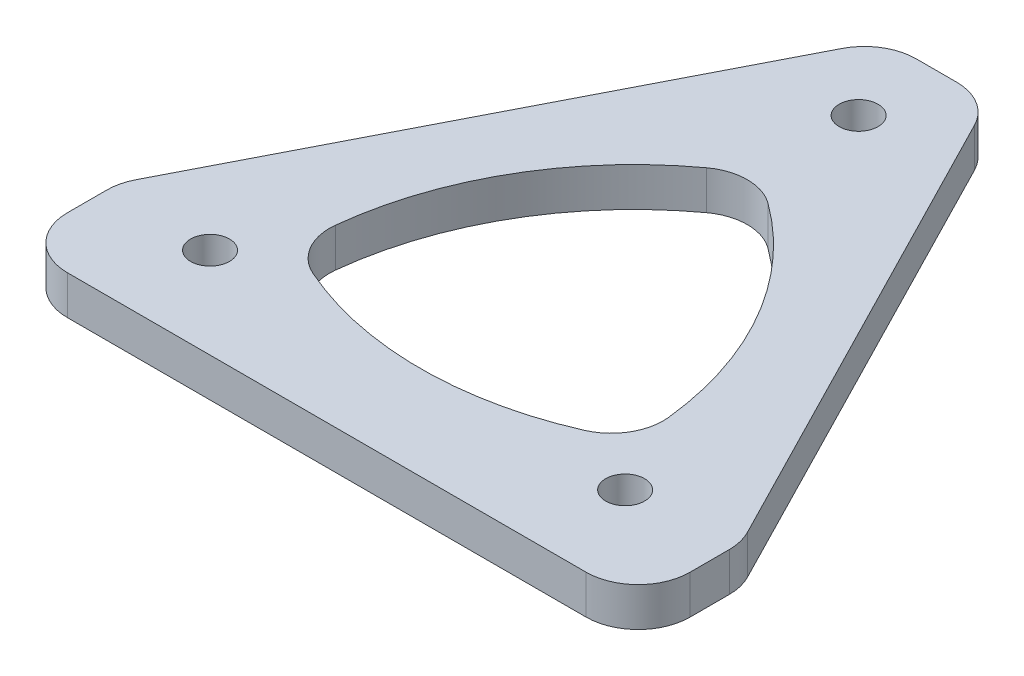
SolidWorks part; units mm, degrees
ref_plane "Front Plane" through (0, 0, 0) normal (0, 0, 1) x (1, 0, 0)
ref_plane "Top Plane" through (0, 0, 0) normal (0, 1, 0) x (1, 0, 0)
ref_plane "Right Plane" through (0, 0, 0) normal (1, 0, 0) x (0, 0, -1)
sketch "Sketch1" plane through (0, 0, 0) normal (0, 1, 0) x (1, 0, 0)
  line L0 (0, 0) -> (-20, 0)
  line L1 (-24, 4) -> (-24, 7.0342)
  line L8 (-23.5593, 8.8594) -> (-5.1152, 44.8253)
  line L10 (-1.556, 47) -> (1.556, 47)
  line L11 (5.1152, 44.8253) -> (23.5593, 8.8594)
  line L12 (24, 7.0342) -> (24, 4)
  line L14 (20, 0) -> (0, 0)
  arc A6 (1.556, 47) -> (5.1152, 44.8253) centre (1.556, 43) cw
  arc A8 (-5.1152, 44.8253) -> (-1.556, 47) centre (-1.556, 43) cw
  arc A10 (23.5593, 8.8594) -> (24, 7.0342) centre (20, 7.0342) cw
  arc A11 (24, 4) -> (20, 0) centre (20, 4) cw
  arc A12 (-24, 7.0342) -> (-23.5593, 8.8594) centre (-20, 7.0342) cw
  arc A13 (-20, 0) -> (-24, 4) centre (-20, 4) cw
  circle A14 centre (-16, 7) radius 1.5
  circle A15 centre (0, 41) radius 1.5
  circle A16 centre (16, 7) radius 1.5
  point P2 (0, 47)
  point P8 (20, 6.0649)
  point P9 (0, 0)
  point P10 (0, 0)
  point P11 (-20, 6)
  point P14 (4, 47)
  point P17 (-4, 47)
  point P24 (-24, 8)
  point P27 (-24, 0)
  dimension "D9" = 3
  dimension "D7" = 4
  dimension "D2" = 47
  dimension "D3" = 24
  dimension "D4" = 8
  dimension "D5" = 8
  dimension "D6" = 7
  dimension "D10" = 16
  dimension "D11" = 16
  dimension "D12" = 34
extrude "Boss-Extrude1" add sketch "Sketch1" along normal blind 3
sketch "Sketch2" plane through (0, 3, 0) normal (0, 1, 0) x (1, 0, 0)
  line L1 (0, 33.1909) -> (-12.9904, 10.6909) construction
  line L2 (-12.9904, 10.6909) -> (12.9904, 10.6909) construction
  line L3 (12.9904, 10.6909) -> (0, 33.1909) construction
  circle A2 centre (0, 18.1909) radius 7.5 construction
  arc A3 (-12.9904, 10.6909) -> (12.9904, 10.6909) centre (0, 33.1909) ccw
  arc A4 (12.9904, 10.6909) -> (0, 33.1909) centre (-12.9904, 10.6909) ccw
  arc A5 (0, 33.1909) -> (-12.9904, 10.6909) centre (12.9904, 10.6909) ccw
  arc A6 (-25.9808, 33.1909) -> (0, -11.8091) centre (-12.9904, 10.6909) ccw construction
  arc A7 (0, -11.8091) -> (25.9808, 33.1909) centre (12.9904, 10.6909) ccw construction
  arc A8 (25.9808, 33.1909) -> (-25.9808, 33.1909) centre (0, 33.1909) ccw construction
  arc A9 (0, 33.1909) -> (-25.9808, 33.1909) centre (-12.9904, 10.6909) ccw construction
  arc A10 (-25.9808, 33.1909) -> (-12.9904, 10.6909) centre (0, 33.1909) ccw construction
  arc A11 (25.9808, 33.1909) -> (0, 33.1909) centre (12.9904, 10.6909) ccw construction
  arc A12 (12.9904, 10.6909) -> (25.9808, 33.1909) centre (0, 33.1909) ccw construction
  arc A13 (0, -11.8091) -> (12.9904, 10.6909) centre (-12.9904, 10.6909) ccw construction
  arc A14 (-12.9904, 10.6909) -> (0, -11.8091) centre (12.9904, 10.6909) ccw construction
  point P5 (0, 10.6909)
  dimension "D1" = 15
extrude "Cut-Extrude1" cut sketch "Sketch2" against normal blind 3
fillet "Fillet1" radius 4 3 edges at (12.9904, 1.5, -10.6909) (-12.9904, 1.5, -10.6909) (0, 1.5, -33.1909)
